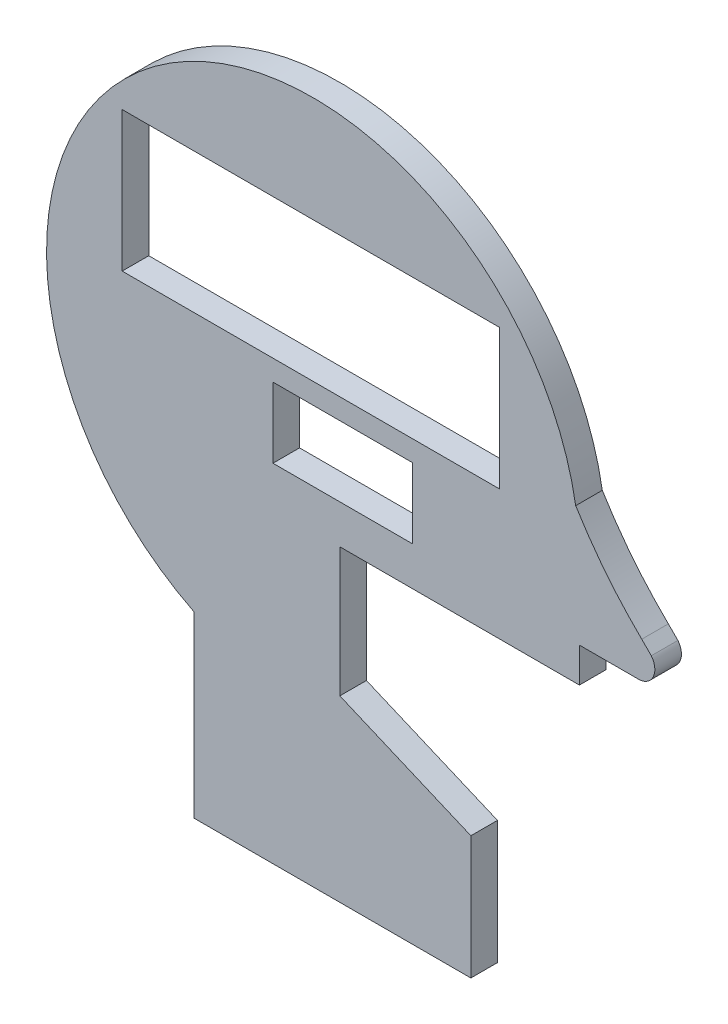
SolidWorks part; units mm, degrees
ref_plane "Front Plane" through (0, 0, 0) normal (0, 0, 1) x (1, 0, 0)
ref_plane "Top Plane" through (0, 0, 0) normal (0, 1, 0) x (1, 0, 0)
ref_plane "Right Plane" through (0, 0, 0) normal (1, 0, 0) x (0, 0, -1)
sketch "Sketch2" plane through (0, 0, 0) normal (0, 0, 1) x (1, 0, 0)
  line L1 (94.1739, -10.9639) -> (96.9079, -13.6978)
  line L2 (93.1975, -21.3545) -> (76.3167, -21.3545)
  line L3 (76.3167, -21.3545) -> (76.3167, -31.2736)
  line L4 (76.3167, -31.2736) -> (7.693, -31.2736)
  line L5 (-34.1298, -68.2597) -> (-34.1298, -119.4807)
  line L6 (-34.1298, -119.4807) -> (45.2246, -119.4807)
  line L7 (45.2246, -119.4807) -> (45.2246, -84.1898)
  line L8 (45.2246, -84.1898) -> (7.693, -68.2597)
  line L9 (7.693, -68.2597) -> (7.693, -31.2736)
  arc A0 (75.2527, 12.6991) -> (-34.1298, -68.2597) centre (0, 0) ccw
  arc A1 (93.1975, -21.3545) -> (96.1268, -12.9167) centre (93.1975, -16.6271) ccw
  spline S0 degree 2 poles (75.2527, 12.6991) (83.2682, -0.4046) (94.1739, -10.9639) knots 0 0 0 1 1 1
  dimension "D1" = 51.221
extrude "Boss-Extrude3" add sketch "Sketch2" along normal blind 7.62 contours S0 A0 L5 L6 L7 L8 L9 L4 L3 L2 A1 L1
sketch "Sketch6" plane through (0, 0, 7.62) normal (0, 0, 1) x (1, 0, 0)
  line L9 (-54.6532, 46.0157) -> (53.4573, 46.0157)
  line L10 (-54.6532, 46.0157) -> (-54.6532, 5.9375)
  line L11 (-54.6532, 5.9375) -> (53.4573, 5.9375)
  line L12 (53.4573, 46.0157) -> (53.4573, 5.9375)
  line L13 (-11.4651, 0) -> (28.482, 0)
  line L14 (-11.4651, 0) -> (-11.4651, -20.1314)
  line L15 (-11.4651, -20.1314) -> (28.482, -20.1314)
  line L16 (28.482, 0) -> (28.482, -20.1314)
extrude "Cut-Extrude5" cut sketch "Sketch6" against normal blind 7.62
